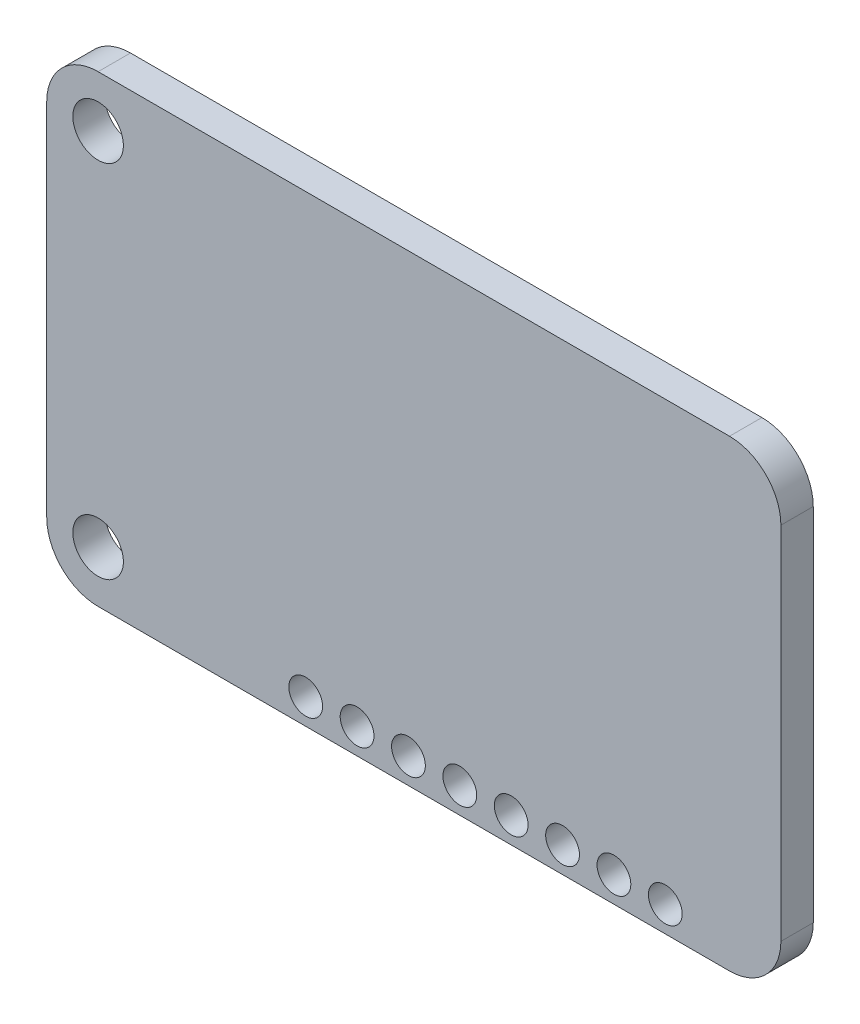
SolidWorks part; units mm, degrees
ref_plane "Front Plane" through (0, 0, 0) normal (0, 0, 1) x (1, 0, 0)
ref_plane "Top Plane" through (0, 0, 0) normal (0, 1, 0) x (1, 0, 0)
ref_plane "Right Plane" through (0, 0, 0) normal (1, 0, 0) x (0, 0, -1)
sketch "Sketch1" plane through (0, 0, 0) normal (0, 0, 1) x (1, 0, 0)
  line L1 (15.61, -11.45) -> (-15.61, -11.45)
  line L2 (18.15, -8.91) -> (18.15, 8.91)
  line L3 (15.61, 11.45) -> (-15.61, 11.45)
  line L4 (-18.15, -8.91) -> (-18.15, 8.91)
  line L5 (18.15, -11.45) -> (-18.15, 11.45) construction
  line L6 (18.15, 11.45) -> (-18.15, -11.45) construction
  arc A0 (15.61, -11.45) -> (18.15, -8.91) centre (15.61, -8.91) ccw
  arc A1 (15.61, 11.45) -> (18.15, 8.91) centre (15.61, 8.91) cw
  arc A2 (-18.15, -8.91) -> (-15.61, -11.45) centre (-15.61, -8.91) ccw
  arc A3 (-18.15, 8.91) -> (-15.61, 11.45) centre (-15.61, 8.91) cw
  circle A4 centre (-15.61, 8.91) radius 1.25
  circle A5 centre (-15.61, -8.91) radius 1.25
  point P0 (0, 0)
  dimension "D3" = 2.54
  dimension "D4" = 2.5
  dimension "D5" = 2.5
  dimension "D1" = 36.3
  dimension "D2" = 22.9
extrude "Boss-Extrude1" add sketch "Sketch1" along normal blind 1.6
sketch "Sketch2" plane through (0, 0, 1.6) normal (0, 0, 1) x (1, 0, 0)
  line L0 (18.15, -8.91) -> (18.15, 8.91) construction
  line L1 (-15.61, -11.45) -> (15.61, -11.45) construction
  circle A0 centre (12.4347, -10.18) radius 0.835
  circle A1 centre (9.8947, -10.18) radius 0.835
  circle A2 centre (7.3547, -10.18) radius 0.835
  circle A3 centre (4.8147, -10.18) radius 0.835
  circle A4 centre (2.2747, -10.18) radius 0.835
  circle A5 centre (-0.2653, -10.18) radius 0.835
  circle A6 centre (-2.8053, -10.18) radius 0.835
  circle A7 centre (-5.3453, -10.18) radius 0.835
  dimension "D1" = 1.67
  dimension "D2" = 5.7153
  dimension "D3" = 1.27
  dimension "D4" = 8
extrude "Cut-Extrude1" cut sketch "Sketch2" against normal blind 10
